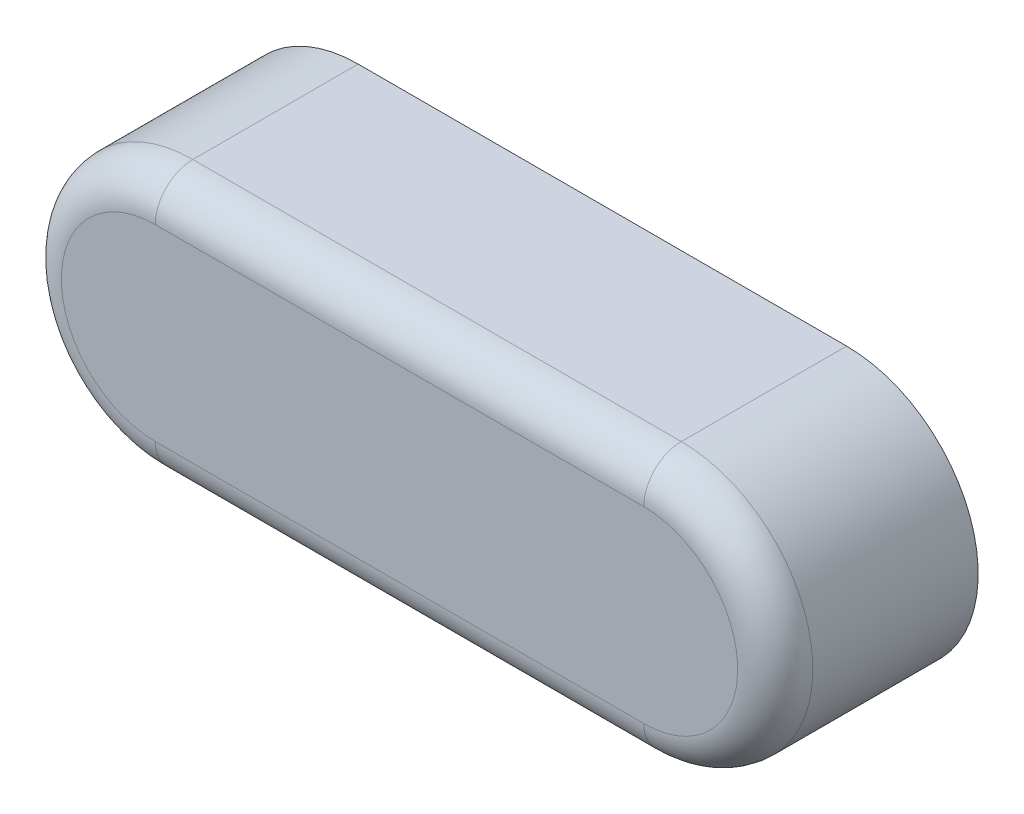
SolidWorks part; units mm, degrees
ref_plane "Front Plane" through (0, 0, 0) normal (0, 0, 1) x (1, 0, 0)
ref_plane "Top Plane" through (0, 0, 0) normal (0, 1, 0) x (1, 0, 0)
ref_plane "Right Plane" through (0, 0, 0) normal (1, 0, 0) x (0, 0, -1)
sketch "Sketch1" plane through (0, 0, 0) normal (0, 0, 1) x (1, 0, 0)
  line L0 (-3.25, 0) -> (3.25, 0) construction
  line L1 (-3.25, 1.75) -> (3.25, 1.75)
  line L2 (-3.25, -1.75) -> (3.25, -1.75)
  arc A0 (-3.25, 1.75) -> (-3.25, -1.75) centre (-3.25, 0) ccw
  arc A1 (3.25, -1.75) -> (3.25, 1.75) centre (3.25, 0) ccw
  point P3 (0, 0)
  dimension "D1" = 10
  dimension "D2" = 3.5
extrude "Boss-Extrude1" add sketch "Sketch1" along normal blind 2.7
fillet "Fillet1" radius 0.5 4 edges at (5, 0, 2.7) (0, -1.75, 2.7) (-5, 0, 2.7) (0, 1.75, 2.7)
